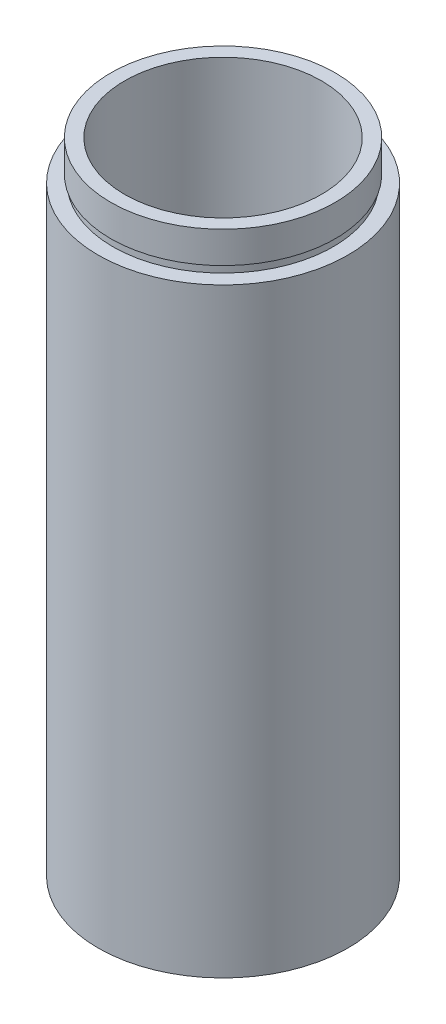
SolidWorks part; units mm, degrees
ref_plane "前视基准面" through (0, 0, 0) normal (0, 0, 1) x (1, 0, 0)
ref_plane "上视基准面" through (0, 0, 0) normal (0, 1, 0) x (1, 0, 0)
ref_plane "右视基准面" through (0, 0, 0) normal (1, 0, 0) x (0, 0, -1)
sketch "草图1" plane through (0, 0, 0) normal (0, 0, 1) x (1, 0, 0)
  line L0 (0, 161.3762) -> (0, 0) construction
  line L1 (141.7365, 0) -> (-131.7984, 0) construction
  line L2 (14.25, 0) -> (14.25, 4.5)
  line L3 (15.85, 0) -> (15.85, 76.2)
  line L4 (14.25, 0) -> (15.85, 0)
  line L5 (14.35, 4.5) -> (14.35, 5.5)
  line L6 (14.25, 4.5) -> (14.35, 4.5)
  line L7 (12.5, 5.5) -> (12.5, 81.2)
  line L8 (12.5, 5.5) -> (14.35, 5.5)
  line L9 (14.25, 81.2) -> (14.25, 77.2)
  line L10 (12.5, 81.2) -> (14.25, 81.2)
  line L11 (14, 77.2) -> (14, 76.2)
  line L12 (14, 77.2) -> (14.25, 77.2)
  line L13 (14, 76.2) -> (15.85, 76.2)
  point P7 (14.25, 2.25)
  dimension "D1" = 14.25
  dimension "D2" = 4.5
  dimension "D3" = 15.85
  dimension "D4" = 14.35
  dimension "D5" = 12.5
  dimension "D6" = 1
  dimension "D7" = 76.2
  dimension "D8" = 14.25
  dimension "D9" = 14
  dimension "D10" = 5
  dimension "D11" = 1
revolve "旋转1" add sketch "草图1" angle 360 about L0
cosmetic thread "装饰螺纹线1"
cosmetic thread "装饰螺纹线2"
cosmetic thread "装饰螺纹线3"
